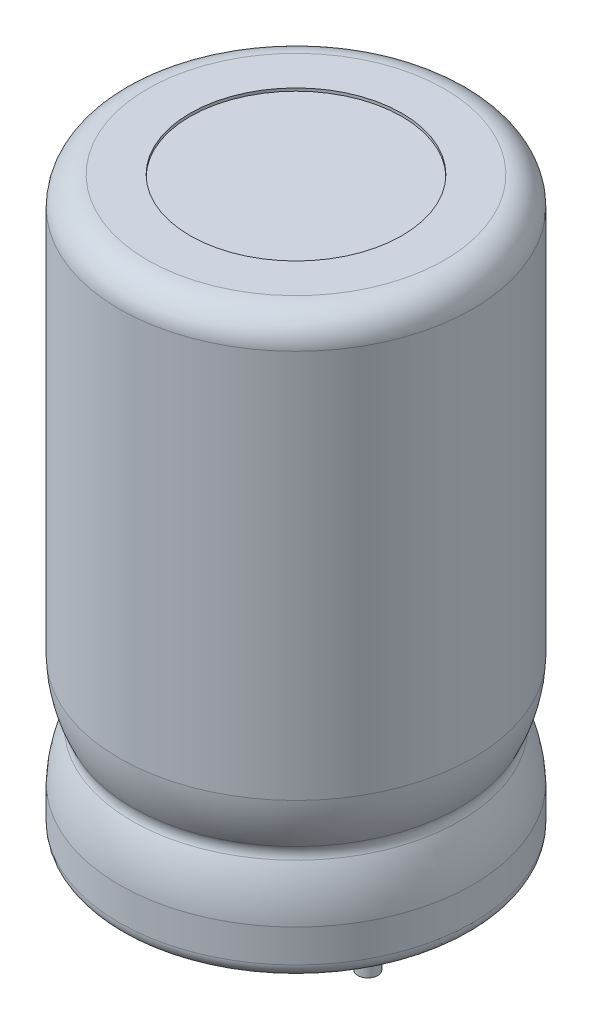
SolidWorks part; units mm, degrees
ref_plane "Front Plane" through (0, 0, 0) normal (0, 0, 1) x (1, 0, 0)
ref_plane "Top Plane" through (0, 0, 0) normal (0, 1, 0) x (1, 0, 0)
ref_plane "Right Plane" through (0, 0, 0) normal (1, 0, 0) x (0, 0, -1)
sketch "Sketch2" plane through (0, 0, 0) normal (0, 1, 0) x (1, 0, 0)
  circle A0 centre (0, 0) radius 0.35
  dimension "D1" = 0.7
extrude "Base-Extrude" add sketch "Sketch2" against normal blind 3
sketch "Sketch3" plane through (0, 0, 0) normal (0, 1, 0) x (-1, 0, 0)
  line L0 (0, 0) -> (3.6061, 0) construction
  circle A0 centre (2.54, 0) radius 3.75
  dimension "D1" = 7.5
  dimension "D2" = 1.21
extrude "Boss-Extrude1" add sketch "Sketch3" along normal blind 0.5
ref_plane "Plane5" through (0, -0.1, 0) normal (0, 1, 0) x (-1, 0, 0)
sketch "Sketch4" plane through (0, 0, 0) normal (0, -1, 0) x (1, 0, 0)
  line L0 (0, 0) -> (-6.29, 0) construction
  circle A0 centre (-5.08, 0) radius 0.35
  circle A1 centre (0, 0) radius 0.35 construction
  circle A2 centre (-2.54, 0) radius 3.75 construction
  dimension "D1" = 0.86
extrude "Boss-Extrude2" add sketch "Sketch4" along normal blind 3
sketch "Sketch5" plane through (0, -0.1, 0) normal (0, -1, 0) x (1, 0, 0)
  circle A2 centre (-2.54, 0) radius 6.25
  dimension "D1" = 12.5
extrude "Boss-Extrude4" add sketch "Sketch5" along normal blind 0.1 and the other way blind 20.2
sketch "Sketch7" plane through (0, -0.2, 0) normal (0, -1, 0) x (1, 0, 0)
  circle A0 centre (-2.54, 0) radius 3.75
  circle A1 centre (-2.54, 0) radius 6.25 construction
  circle A2 centre (-5.08, 0) radius 0.35 construction
  circle A3 centre (-5.08, 0) radius 0.35
  circle A4 centre (0, 0) radius 0.35 construction
  circle A5 centre (0, 0) radius 0.35
  dimension "D1" = 7.5
extrude "Cut-Extrude3" cut sketch "Sketch7" against normal blind 0.1
fillet "Fillet1" radius 0.5 1 edges at (-2.54, -0.2, -6.25)
fillet "Fillet2" radius 1 1 edges at (-2.54, 20.1, -6.25)
sketch "Sketch8" plane through (0, 20.1, 0) normal (0, 1, 0) x (-1, 0, 0)
  circle A0 centre (2.54, 0) radius 3.75
  circle A1 centre (2.54, 0) radius 5.25 construction
  dimension "D1" = 7.5
extrude "Cut-Extrude4" cut sketch "Sketch8" against normal blind 0.1
sketch "Sketch10" plane through (0, 0, 0) normal (0, 0, 1) x (1, 0, 0)
  line L0 (3.21, 7.4095) -> (3.21, 2.4608) construction
  line L1 (3.71, 0.3) -> (3.71, 19.1) construction
  line L2 (-15.3153, 3.4) -> (14.5322, 3.4) construction
  line L3 (-12.6019, 5.69) -> (11.1728, 5.69) construction
  line L4 (-10.6637, 1.11) -> (8.5886, 1.11) construction
  line L5 (3.26, 6.8462) -> (3.26, 0.5732) construction
  line L6 (1.3626, 3.61) -> (4.5908, 3.61) construction
  line L7 (1.3626, 3.19) -> (5.1778, 3.19) construction
  line L8 (-2.54, 0.3463) -> (-2.54, 10.6426) construction
  line L9 (-2.54, 0.3) -> (-2.54, 19.1) construction
  line L11 (3.71, 5.69) -> (4.21, 5.69)
  line L13 (3.71, 1.11) -> (4.21, 1.11)
  line L14 (4.21, 5.69) -> (4.21, 1.11)
  arc A0 (3.26, 3.61) -> (3.26, 3.19) centre (3.676, 3.4) ccw
  arc A1 (3.71, 5.69) -> (3.26, 3.61) centre (-0.5141, 5.5152) cw
  arc A2 (3.26, 3.19) -> (3.71, 1.11) centre (-0.5141, 1.2848) cw
  dimension "D8" = 0.5
  dimension "D1" = 0.5
  dimension "D2" = 3.4
  dimension "D3" = 5.69
  dimension "D4" = 1.11
  dimension "D5" = 3.26
  dimension "D6" = 0.42
  dimension "D7" = 0.21
revolve "Cut-Revolve1" cut sketch "Sketch10" angle 360 about L8
ref_plane "Board Plane" through (0, -0.5, 0) normal (0, 1, 0) x (-1, 0, 0)
sketch "Component_Outline" plane through (0, -0.5, 0) normal (0, 1, 0) x (-1, 0, 0)
  circle A0 centre (2.54, 0) radius 6.25
  circle A1 centre (2.54, 0) radius 6.25 construction
  point P4 (0, 0)
